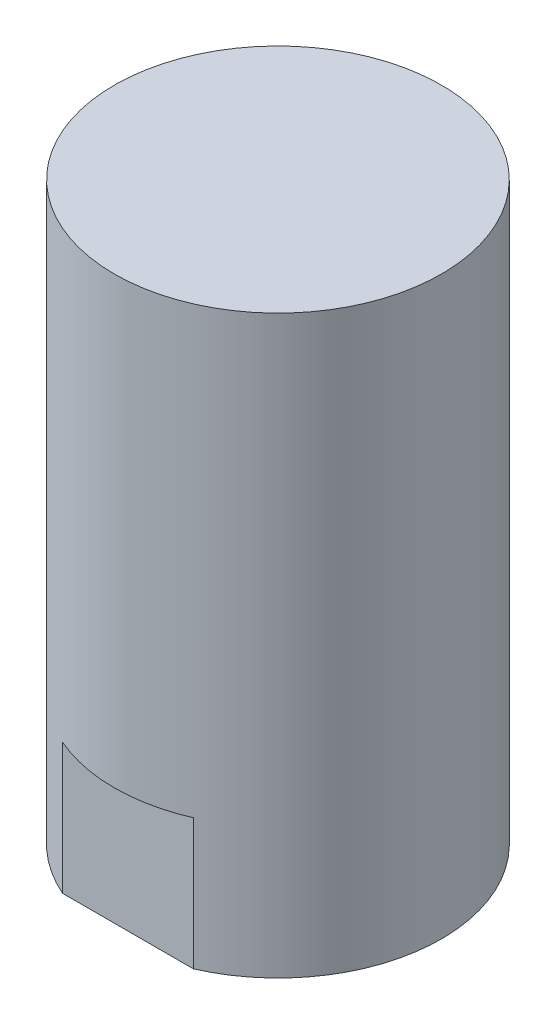
SolidWorks part; units mm, degrees
ref_plane "Front Plane" through (0, 0, 0) normal (0, 0, 1) x (1, 0, 0)
ref_plane "Top Plane" through (0, 0, 0) normal (0, 1, 0) x (1, 0, 0)
ref_plane "Right Plane" through (0, 0, 0) normal (1, 0, 0) x (0, 0, -1)
sketch "Sketch1" plane through (0, 0, 0) normal (0, 1, 0) x (1, 0, 0)
  circle A0 centre (0, 0) radius 12.5
  dimension "D1" = 25
extrude "Boss-Extrude1" add sketch "Sketch1" along normal blind 44
sketch "Sketch3" plane through (0, 0, 0) normal (0, -1, 0) x (1, 0, 0)
  line L0 (-5, 11.4564) -> (5, 11.4564)
  circle A0 centre (0, 0) radius 5
  arc A3 (5, 11.4564) -> (-5, 11.4564) centre (0, 0) ccw
  arc A4 (-5, 11.4564) -> (5, 11.4564) centre (0, 0) ccw construction
  dimension "D1" = 10
  dimension "D2" = 25
  dimension "D3" = 10
extrude "Cut-Extrude1" cut sketch "Sketch3" against normal blind 10
